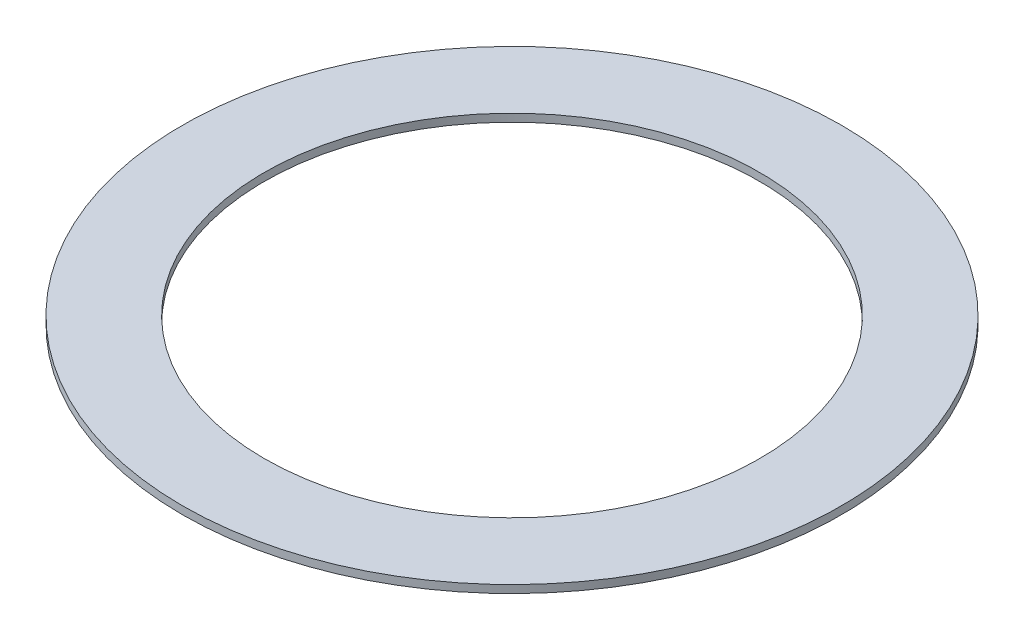
SolidWorks part; units mm, degrees
material "Oak"
ref_plane "Front Plane" through (0, 0, 0) normal (0, 0, 1) x (1, 0, 0)
ref_plane "Top Plane" through (0, 0, 0) normal (0, 1, 0) x (1, 0, 0)
ref_plane "Right Plane" through (0, 0, 0) normal (1, 0, 0) x (0, 0, -1)
sketch "Sketch1" plane through (0, 0, 0) normal (0, 1, 0) x (1, 0, 0)
  circle A0 centre (0, 0) radius 76.2
  circle A1 centre (0, 0) radius 101.346
  dimension "D1" = 152.4
  dimension "D2" = 202.692
extrude "Boss-Extrude1" add sketch "Sketch1" along normal blind 2.4
